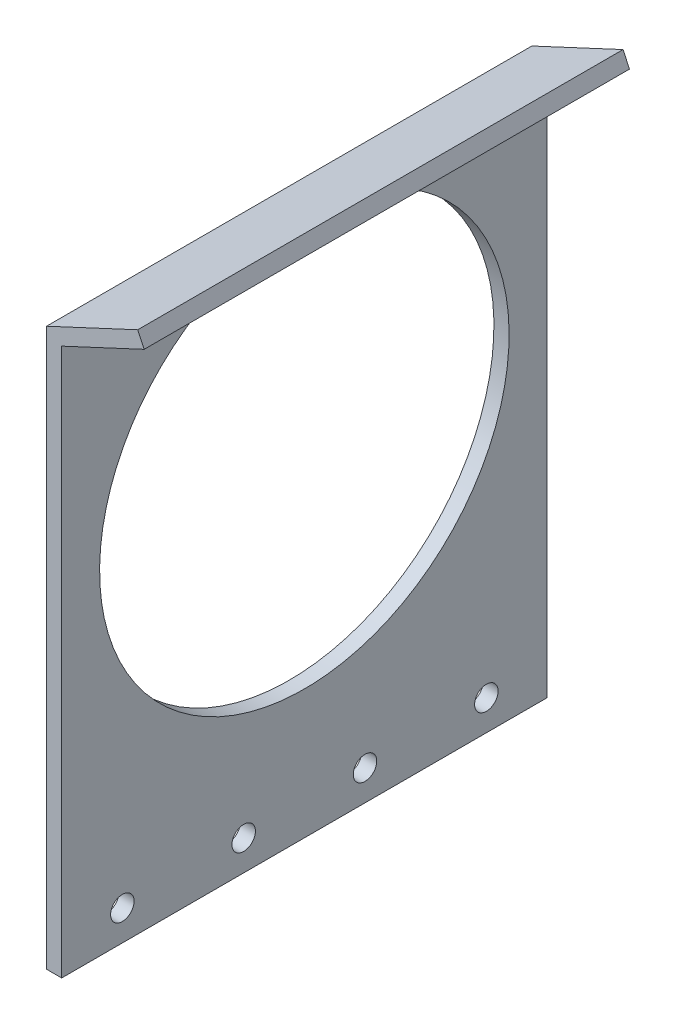
SolidWorks part; units mm, degrees
material "6061-T6 (SS)"
ref_plane "Front Plane" through (0, 0, 0) normal (0, 0, 1) x (1, 0, 0)
ref_plane "Top Plane" through (0, 0, 0) normal (0, 1, 0) x (1, 0, 0)
ref_plane "Right Plane" through (0, 0, 0) normal (1, 0, 0) x (0, 0, -1)
sketch "Sketch1" plane through (0, 0, 0) normal (0, 0, 1) x (1, 0, 0)
  line L0 (0, 0) -> (0, 116.5767)
  line L1 (0, 116.5767) -> (19.0984, 125.4824)
  line L2 (19.0984, 125.4824) -> (20.4402, 122.6049)
  line L3 (20.4402, 122.6049) -> (3.175, 114.554)
  line L4 (3.175, 114.554) -> (3.175, 0)
  line L5 (3.175, 0) -> (0, 0)
  dimension "D1" = 114.554
  dimension "D2" = 3.175
  dimension "D3" = 115
  dimension "D4" = 3.175
  dimension "D5" = 19.05
extrude "Boss-Extrude1" add sketch "Sketch1" along normal blind 101.6 contours L0 L1 L2 L3 L4 L5
hole_wizard "#10 (0.1935) Diameter Hole1" positions "Sketch3" profile "Sketch2" hole size "#10" standard "ANSI Inch" end condition through all
sketch "Sketch3" plane through (3.175, 0, 0) normal (1, 0, 0) x (0, 0, -1)
  line L1 (-101.6, 0) -> (0, 0) construction
  line L2 (0, 114.554) -> (0, 0) construction
  line L3 (-101.6, 114.554) -> (-101.6, 0) construction
  point P0 (-88.9, 6.35)
  point P2 (-63.5, 6.35)
  point P4 (-38.1, 6.35)
  point P6 (-12.7, 6.35)
  dimension "D1" = 6.35
  dimension "D2" = 12.7
  dimension "D3" = 12.7
  dimension "D4" = 25.4
  dimension "D5" = 25.4
sketch "Sketch2" plane through (3.175, 6.35, 88.9) normal (0, 1, 0) x (0, 0, -1)
  line L0 (0, 0) -> (0, 3.175)
  line L1 (0, 3.175) -> (2.4574, 3.175)
  line L2 (2.4574, 3.175) -> (2.4574, 0)
  line L5 (2.4574, 0) -> (0, 0)
  line L11 (0, -6.35) -> (0, 107.95) construction
  dimension "Thru Hole Dia." = 4.9149
  dimension "Thru Hole Depth" = 3.175
sketch "Sketch4" plane through (3.175, 0, 0) normal (1, 0, 0) x (0, 0, -1)
  line L0 (-101.6, 0) -> (0, 0) construction
  line L4 (-101.6, 114.554) -> (-101.6, 0) construction
  circle A0 centre (-50.8, 69.85) radius 42.8625
  dimension "D1" = 85.725
  dimension "D2" = 69.85
  dimension "D3" = 50.8
extrude "Cut-Extrude1" cut sketch "Sketch4" against normal blind 127
